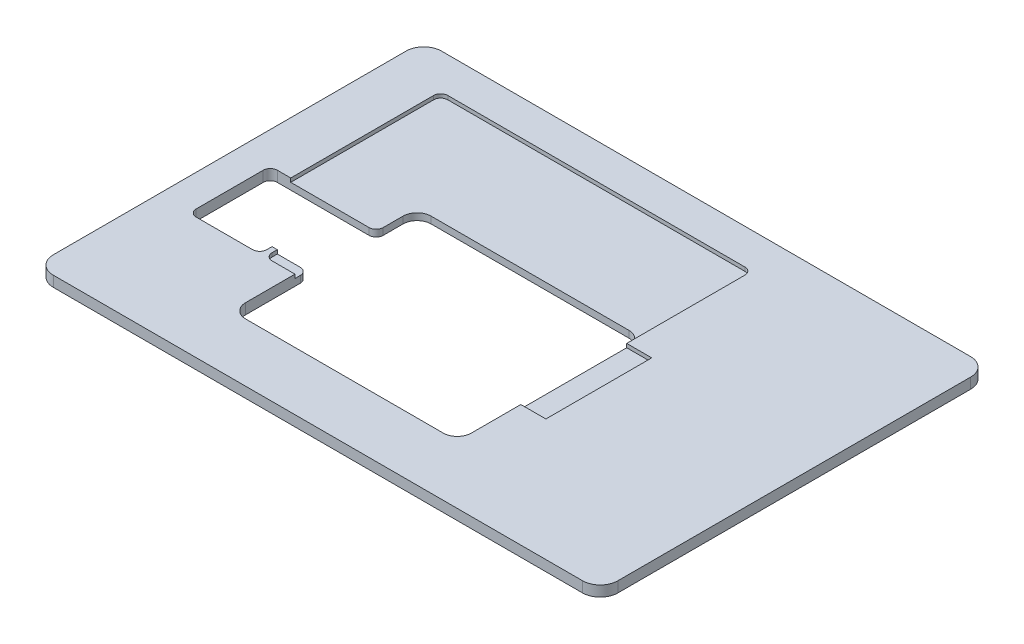
SolidWorks part; units mm, degrees
ref_plane "Front Plane" through (0, 0, 0) normal (0, 0, 1) x (1, 0, 0)
ref_plane "Top Plane" through (0, 0, 0) normal (0, 1, 0) x (1, 0, 0)
ref_plane "Right Plane" through (0, 0, 0) normal (1, 0, 0) x (0, 0, -1)
sketch "Sketch2" plane through (0, 0, 0) normal (0, 1, 0) x (1, 0, 0)
  line L1 (-80, 55) -> (80, 55)
  line L2 (-80, 55) -> (-80, -55)
  line L3 (-80, -55) -> (80, -55)
  line L4 (80, 55) -> (80, -55)
  line L5 (-80, 55) -> (80, -55) construction
  line L6 (-80, -55) -> (80, 55) construction
  point P0 (0, 0)
  dimension "D1" = 160
  dimension "D2" = 110
extrude "Boss-Extrude1" add sketch "Sketch2" along normal mid plane 3
fillet "Fillet1" radius 5 4 edges at (-80, 0, 55) (-80, 0, -55) (80, 0, -55) (80, 0, 55)
sketch "Sketch3" plane through (0, 1.5, 0) normal (0, 1, 0) x (1, 0, 0)
  line L0 (-80, 50) -> (-80, -50) construction
  line L1 (-71, 2.5) -> (-51, 2.5)
  line L2 (-71, 2.5) -> (-71, -20.5)
  line L3 (-71, -20.5) -> (-51, -20.5)
  line L4 (-51, -17) -> (-51, -20.5)
  line L5 (-71, 2.5) -> (-51, -20.5) construction
  line L6 (-71, -20.5) -> (-51, 2.5) construction
  line L7 (-75, -55) -> (75, -55) construction
  line L8 (-41, -17) -> (-49.93, -17)
  line L9 (-51, -20.5) -> (-49.93, -20.5) construction
  line L10 (-51, -20.5) -> (-51, -17) construction
  line L11 (-51, -17) -> (-49.93, -17)
  line L12 (-49.93, -20.5) -> (-49.93, -17) construction
  line L13 (-41, -17) -> (-41, -38.5)
  line L14 (-41, -38.5) -> (23, -38.5)
  line L15 (23, -38.5) -> (23, 14.1)
  line L16 (23, 14.1) -> (-41, 14.1)
  line L17 (-41, 14.1) -> (-41, 2.5)
  line L18 (-41, 2.5) -> (-51, 2.5)
  line L19 (-51, 2.5) -> (-51, -17) construction
  point P0 (-61, -9)
  point P12 (-50.465, -20.5)
  dimension "D1" = 9
  dimension "D2" = 20
  dimension "D3" = 23
  dimension "D4" = 34.5
  dimension "D5" = 1.07
  dimension "D6" = 3.5
  dimension "D7" = 64
  dimension "D8" = 21.5
  dimension "D9" = 10
  dimension "D10" = 30
  dimension "D11" = 52.6
extrude "Cut-Extrude1" cut sketch "Sketch3" against normal through all
fillet "Fillet2" radius 2 5 edges at (-41, 0, -2.5) (-51, 0, 20.5) (-71, 0, 20.5) (-71, 0, -2.5) (-41, 0, 17)
fillet "Fillet3" radius 4 4 edges at (23, 0, -14.1) (23, 0, 38.5) (-41, 0, 38.5) (-41, 0, -14.1)
sketch "Sketch4" plane through (0, 1.5, 0) normal (0, 1, 0) x (1, 0, 0)
  line L0 (-65.2, 2.5) -> (-65.2, 45)
  line L1 (-43, 2.5) -> (-69, 2.5) construction
  line L2 (-71, 0.5) -> (-71, -18.5) construction
  line L3 (-49.5, 2.5) -> (-65.2, 2.5)
  line L4 (-65.2, 2.5) -> (-69, 2.5) construction
  line L5 (19, 14.1) -> (-37, 14.1) construction
  line L6 (-41, 10.1) -> (-41, 4.5) construction
  line L7 (-41, 10.1) -> (-41, 9.5)
  line L8 (19, 14.1) -> (-37, 14.1)
  line L9 (23, 10.1) -> (23, 45)
  line L10 (23, 45) -> (-65.2, 45)
  line L11 (-51, -18.5) -> (-51, -17) construction
  line L12 (-41, 9.5) -> (30.1, 9.5)
  line L13 (-49.5, 2.5) -> (-49.5, -20.5)
  line L14 (-49.5, -20.5) -> (30.1, -20.5)
  line L15 (30.1, 9.5) -> (30.1, -20.5)
  line L16 (-41, 6.2965) -> (30.1, -20.5) construction
  line L17 (-49.5, -20.5) -> (30.1, 9.5) construction
  line L18 (-69, -20.5) -> (-53, -20.5) construction
  line L19 (-49.5, 9.5) -> (-41, 9.5) construction
  line L20 (-49.5, 9.5) -> (-41, 6.2965) construction
  line L21 (-49.5, 9.5) -> (-49.5, 2.5) construction
  line L22 (-41, 9.5) -> (-41, 6.2965) construction
  line L23 (-41, 6.2965) -> (-41, 4.5) construction
  line L24 (-43, 2.5) -> (-49.5, 2.5) construction
  arc A1 (-37, 14.1) -> (-41, 10.1) centre (-37, 10.1) ccw construction
  arc A2 (-37, 14.1) -> (-41, 10.1) centre (-37, 10.1) ccw
  arc A3 (23, 10.1) -> (19, 14.1) centre (19, 10.1) ccw construction
  arc A4 (23, 10.1) -> (19, 14.1) centre (19, 10.1) ccw
  point P6 (-9.7, -5.5)
  dimension "D1" = 5.8
  dimension "D2" = 42.5
  dimension "D3" = 79.6
  dimension "D4" = 1.5
  dimension "D5" = 30
extrude "Cut-Extrude2" cut sketch "Sketch4" against normal blind 1.07
fillet "Fillet4" radius 2 3 edges at (-49.5, 0.965, 20.5) (23, 0.965, -45) (-65.2, 0.965, -45)
equation "\"∩╗┐cas_w\" = 38.1mm"
equation "\"cas_l\" = 83.0mm"
equation "\"cas_h\" = 280.0mm"
equation "\"rail_w\" = 50.5mm"
equation "\"rail_c\" = 10.5mm"
equation "\"stinset_l\" = 160mm"
equation "\"stinset_w\" = 110mm"
equation "\"stinset_h\" = 3mm"
equation "\"stinset_fillet\" = 5mm"
equation "\"slide_l\" = 75.6mm"
equation "\"slide_w\" = 26mm"
equation "\"slide_h\" = 1.07mm"
equation "\"slide_fillet\" = 1mm"
equation "\"D1@Sketch2\"=\"stinset_l\""
equation "\"D2@Sketch2\"=\"stinset_w\""
equation "\"D1@Boss-Extrude1\"=\"stinset_h\""
equation "\"D1@Fillet1\"=\"stinset_fillet\""
equation "\"D3@Sketch4\"=\"slide_l\"+4mm"
equation "\"D5@Sketch4\"=\"slide_w\"+4mm"
equation "\"D1@Cut-Extrude2\"=\"slide_h\""
